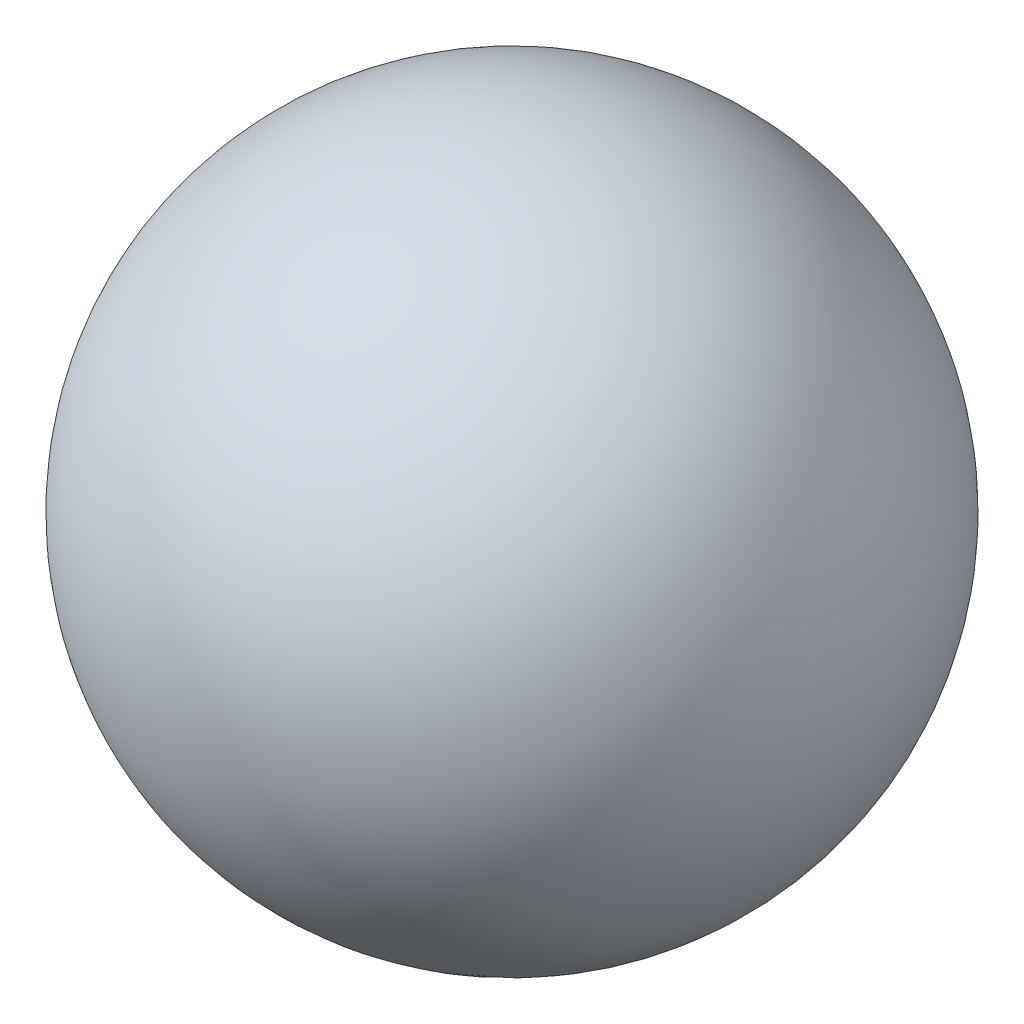
SolidWorks part; units mm, degrees
material "Rubber"
ref_plane "Front Plane" through (0, 0, 0) normal (0, 0, 1) x (1, 0, 0)
ref_plane "Top Plane" through (0, 0, 0) normal (0, 1, 0) x (1, 0, 0)
ref_plane "Right Plane" through (0, 0, 0) normal (1, 0, 0) x (0, 0, -1)
sketch "Sketch2" plane through (0, 0, 0) normal (0, 1, 0) x (1, 0, 0)
  line L0 (0, -20) -> (0, 20)
  arc A0 (0, 20) -> (0, -20) centre (0, 0) ccw
  point P6 (0, 0)
  dimension "D1" = 20
revolve "Revolve1" add sketch "Sketch2" angle 360 about L0
sketch "Sketch3" plane through (0, 0, 0) normal (0, 1, 0) x (1, 0, 0)
  line L1 (-6.5, -12.5) -> (6.5, -12.5)
  line L2 (-6.5, -12.5) -> (-6.5, 12.5)
  line L3 (-6.5, 12.5) -> (6.5, 12.5)
  line L4 (6.5, -12.5) -> (6.5, 12.5)
  line L5 (-6.5, -12.5) -> (6.5, 12.5) construction
  line L6 (-6.5, 12.5) -> (6.5, -12.5) construction
  point P0 (0, 0)
  dimension "D1" = 25
  dimension "D2" = 13
extrude "Cut-Extrude1" cut sketch "Sketch3" against normal blind 27
fillet "Fillet1" radius 4 4 edges at (-6.5, -7.0975, 12.5) (6.5, -7.0975, 12.5) (6.5, -7.0975, -12.5) (-6.5, -7.0975, -12.5)
